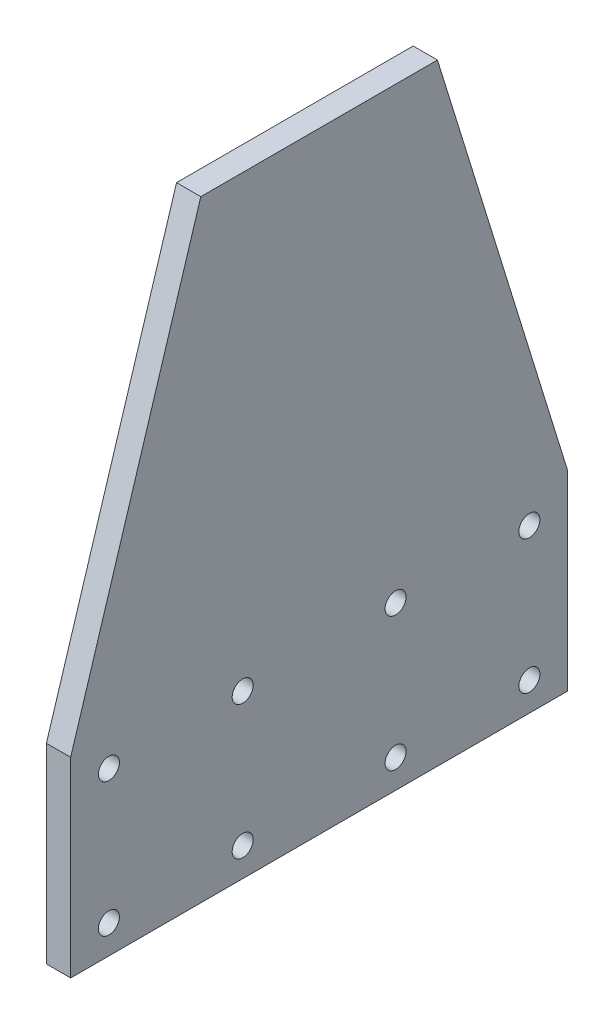
SolidWorks part; units mm, degrees
ref_plane "Front Plane" through (0, 0, 0) normal (0, 0, 1) x (1, 0, 0)
ref_plane "Top Plane" through (0, 0, 0) normal (0, 1, 0) x (1, 0, 0)
ref_plane "Right Plane" through (0, 0, 0) normal (1, 0, 0) x (0, 0, -1)
sketch "Sketch2" plane through (0, 0, 0) normal (1, 0, 0) x (0, 0, -1)
  line L0 (34.0476, 160) -> (95.9524, 160)
  line L1 (0, 0) -> (130, 0)
  line L2 (0, 0) -> (0, 50)
  line L3 (0, 50) -> (34.0476, 160)
  line L4 (65, 0) -> (65, 160) construction
  line L5 (34.0476, 160) -> (65, 260) construction
  line L6 (65, 160) -> (65, 260) construction
  line L7 (130, 50) -> (95.9524, 160)
  line L8 (130, 0) -> (130, 50)
  dimension "D1" = 65
  dimension "D2" = 50
  dimension "D3" = 260
  dimension "D4" = 100
extrude "Boss-Extrude1" add sketch "Sketch2" along normal blind 6.35
sketch "Sketch3" plane through (6.35, 0, 0) normal (1, 0, 0) x (0, 0, -1)
  line L0 (10, 42.5) -> (45, 7.5) construction
  line L1 (45, 7.5) -> (10, 7.5) construction
  line L2 (10, 7.5) -> (45, 42.5) construction
  line L3 (45, 42.5) -> (10, 42.5) construction
  line L4 (10, 42.5) -> (10, 7.5) construction
  line L5 (0, 50) -> (0, 0) construction
  line L6 (65, 160) -> (65, 0) construction
  line L7 (95.9524, 160) -> (34.0476, 160) construction
  line L8 (0, 0) -> (130, 0) construction
  circle A0 centre (10, 42.5) radius 2.75
  circle A1 centre (45, 42.5) radius 2.75
  circle A2 centre (10, 7.5) radius 2.75
  circle A3 centre (45, 7.5) radius 2.75
  circle A4 centre (120, 7.5) radius 2.75
  circle A5 centre (85, 7.5) radius 2.75
  circle A6 centre (85, 42.5) radius 2.75
  circle A7 centre (120, 42.5) radius 2.75
  point P12 (27.5, 25)
  point P13 (10, 25)
  point P15 (0, 25)
  dimension "D1" = 5.5
  dimension "D2" = 35
  dimension "D3" = 10
extrude "Cut-Extrude1" cut sketch "Sketch3" against normal through all
